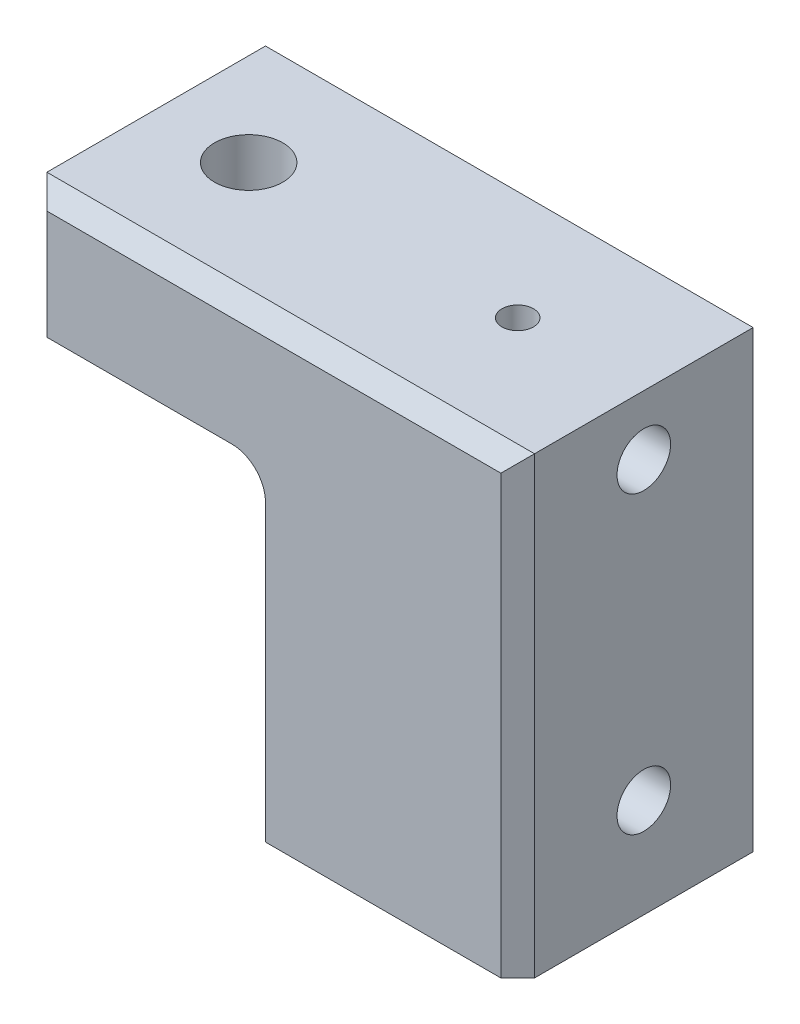
SolidWorks part; units mm, degrees
material "6061-T6 Al"
ref_plane "Front" through (0, 0, 0) normal (0, 0, 1) x (1, 0, 0)
ref_plane "Top" through (0, 0, 0) normal (0, 1, 0) x (1, 0, 0)
ref_plane "Right" through (0, 0, 0) normal (1, 0, 0) x (0, 0, -1)
sketch "Sketch1" plane through (0, 0, 0) normal (0, 0, 1) x (1, 0, 0)
  line L0 (-73.66, 49.53) -> (-73.66, 68.58)
  line L1 (-73.66, 68.58) -> (0, 68.58)
  line L2 (0, 68.58) -> (0, 0)
  line L3 (0, 0) -> (-38.1, 0)
  line L4 (-38.1, 0) -> (-38.1, 49.53)
  line L5 (-38.1, 49.53) -> (-73.66, 49.53)
  dimension "D1" = 19.05
  dimension "D2" = 38.1
  dimension "D3" = 73.66
  dimension "D4" = 68.58
extrude "Extrude1" add sketch "Sketch1" along normal blind 38.1
hole_wizard "3/8 Clearance Hole1" positions "3DSketch1" profile "Sketch2" hole size "3/8" standard "Ansi Inch" end condition through all
sketch3d "3DSketch1"
  line L0 (-73.66, 68.58, 19.05) -> (-25.1998, 68.58, 19.05) construction
  line L1 (-73.66, 68.58, 38.1) -> (-73.66, 68.58, 0) construction
  point P0 (-59.69, 68.58, 19.05)
  dimension "D1" = 13.97
sketch "Sketch2" plane through (-59.69, 68.58, 19.05) normal (1, 0, 0) x (0, 0, 1)
  line L0 (0, 0) -> (0, 68.58)
  line L1 (0, 68.58) -> (5.1587, 68.58)
  line L2 (5.1587, 68.58) -> (5.1587, 0)
  line L5 (5.1587, 0) -> (0, 0)
  line L11 (0, -6.35) -> (0, 107.95) construction
  dimension "Thru Hole Dia." = 10.3175
  dimension "Thru Hole Depth" = 68.58
hole_wizard "Tapped Hole for 1/4-20 Helicoil3" positions "3DSketch2" profile "Sketch3" tap size "1/4-20" standard "Helicoil® Inch"
sketch3d "3DSketch2"
  line L11 (0, 59.563, 19.05) -> (-180.3654, 59.563, 19.05) construction
  line L14 (0, 68.58, 19.05) -> (0, 0, 19.05) construction
  line L15 (0, 68.58, 38.1) -> (0, 68.58, 0) construction
  line L16 (0, 0, 38.1) -> (0, 0, 0) construction
  point P0 (0, 59.563, 19.05)
  dimension "D1" = 10.033
sketch "Sketch3" plane through (0, 59.563, 19.05) normal (0, 1, 0) x (0, 0, -1)
  line L0 (0, 0) -> (0, 24.8898)
  line L1 (0, 24.8898) -> (3.3782, 22.86)
  line L2 (3.3782, 22.86) -> (3.3782, 15.748)
  line L3 (3.3782, 15.748) -> (4.0475, 15.748)
  line L4 (4.0475, 15.748) -> (4.0475, 0)
  line L5 (4.0475, 0) -> (0, 0)
  line L10 (0, 24.8898) -> (-3.3782, 22.86) construction
  line L11 (0, -6.35) -> (0, 107.95) construction
  dimension "Tap Drill Dia." = 6.7564
  dimension "Tap Drill Depth" = 22.86
  dimension "Thread Major Dia." = 8.095
  dimension "Thread Depth" = 15.748
  dimension "Drill Angle" = 118
hole_wizard "Tapped Hole for 1/4-20 Helicoil1" positions "3DSketch4" profile "Sketch5" tap size "1/4-20" standard "Helicoil® Inch" end condition through all
sketch3d "3DSketch4"
  line L0 (0, 68.58, 19.05) -> (0, 0, 19.05) construction
  line L1 (0, 68.58, 38.1) -> (0, 68.58, 0) construction
  line L2 (0, 0, 38.1) -> (0, 0, 0) construction
  circle A2 centre (0, 59.563, 19.05) radius 4.0475 construction
  point P8 (0, 14.986, 19.05)
  point P33 (4.0475, 59.563, 19.05)
  dimension "D1" = 44.577
sketch "Sketch5" plane through (0, 14.986, 19.05) normal (0, 1, 0) x (0, 0, -1)
  line L0 (0, 0) -> (0, 73.66)
  line L1 (0, 73.66) -> (3.3782, 73.66)
  line L3 (3.3782, 73.66) -> (3.3782, 15.748)
  line L4 (3.3782, 15.748) -> (4.0475, 15.748)
  line L5 (4.0475, 15.748) -> (4.0475, 0)
  line L7 (4.0475, 0) -> (0, 0)
  line L11 (0, -6.35) -> (0, 107.95) construction
  dimension "Thru Tap Drill Dia." = 6.7564
  dimension "Thru Tap Drill Depth" = 73.66
  dimension "Thread Major Dia." = 8.095
  dimension "Thread Depth" = 15.748
fillet "Fillet1" radius 5.08 1 edges at (-38.1, 49.53, 19.05)
hole_wizard "3/16 (0.1875) Diameter Hole1" positions "3DSketch3" profile "Sketch4" hole size "3/16" standard "Ansi Inch"
sketch3d "3DSketch3"
  line L2 (0, 68.58, 38.1) -> (0, 68.58, 0) construction
  line L4 (0, 68.58, 19.05) -> (-31.4722, 68.58, 19.05) construction
  point P8 (-19.05, 68.58, 19.05)
  dimension "D1" = 19.05
sketch "Sketch4" plane through (-19.05, 68.58, 19.05) normal (1, 0, 0) x (0, 0, 1)
  line L0 (0, 0) -> (0, 5.6388)
  line L1 (0, 5.6388) -> (2.3812, 5.6388)
  line L2 (2.3812, 5.6388) -> (2.3812, 0)
  line L5 (2.3812, 0) -> (0, 0)
  line L11 (0, -6.35) -> (0, 107.95) construction
  dimension "Thru Hole Dia." = 4.7625
  dimension "Thru Hole Depth" = 5.6388
chamfer "Chamfer1" distance 2.54 angle 45 9 edges at (0, 68.58, 19.05) (-36.83, 68.58, 0) (-73.66, 68.58, 19.05) (-36.83, 68.58, 38.1) (0, 34.29, 0) (0, 34.29, 38.1) (0, 0, 19.05) (-73.66, 59.055, 0) (-73.66, 59.055, 38.1)
